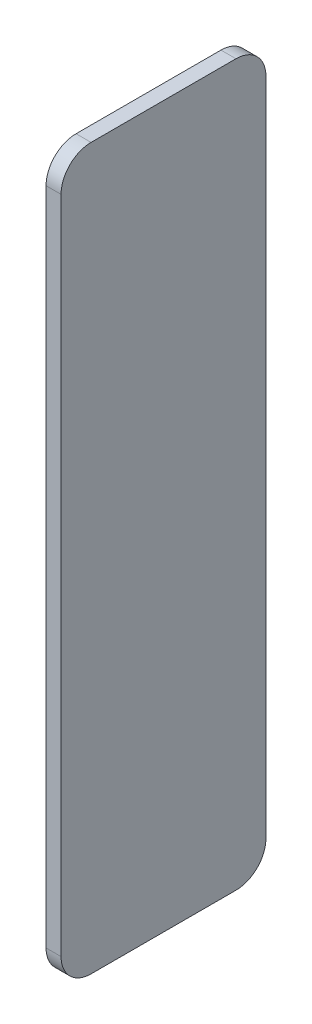
SolidWorks part; units mm, degrees
material "Acrylic (Medium-high impact)"
ref_plane "Front Plane" through (0, 0, 0) normal (0, 0, 1) x (1, 0, 0)
ref_plane "Top Plane" through (0, 0, 0) normal (0, 1, 0) x (1, 0, 0)
ref_plane "Right Plane" through (0, 0, 0) normal (1, 0, 0) x (0, 0, -1)
sketch "Sketch1" plane through (-191.4827, 0, 0) normal (-1, 0, 0) x (0, 0, 1)
  line L1 (-91.0241, 108.7712) -> (-22.7385, 108.7712)
  line L2 (-91.0241, 108.7712) -> (-91.0241, -131.2288)
  line L3 (-91.0241, -131.2288) -> (-22.7385, -131.2288)
  line L4 (-22.7385, 108.7712) -> (-22.7385, -131.2288)
extrude "Boss-Extrude1" add sketch "Sketch1" against normal blind 5
fillet "Fillet1" radius 10 4 edges at (-188.9827, -131.2288, -22.7385) (-188.9827, -131.2288, -91.0241) (-188.9827, 108.7712, -22.7385) (-188.9827, 108.7712, -91.0241)
